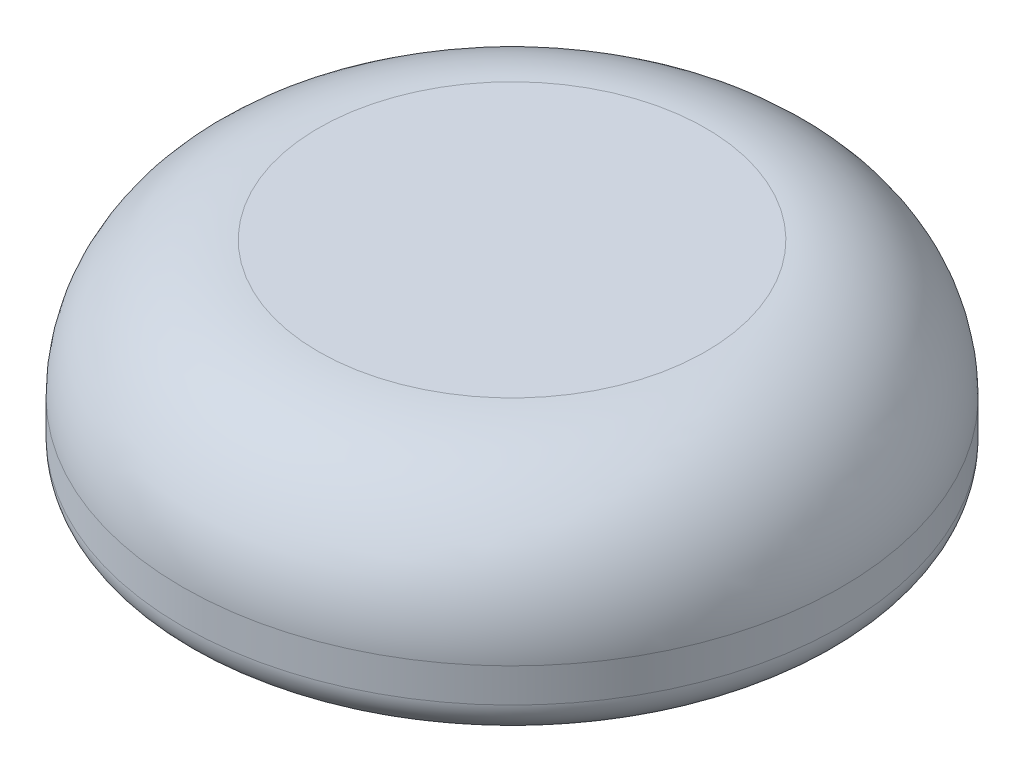
SolidWorks part; units mm, degrees
material "PP Copolymer"
ref_plane "Front Plane" through (0, 0, 0) normal (0, 0, 1) x (1, 0, 0)
ref_plane "Top Plane" through (0, 0, 0) normal (0, 1, 0) x (1, 0, 0)
ref_plane "Right Plane" through (0, 0, 0) normal (1, 0, 0) x (0, 0, -1)
sketch "Sketch3" plane through (0, 0, 0) normal (1, 0, 0) x (0, 0, -1)
  line L0 (12.319, -5.081) -> (12.319, -6.3498)
  line L2 (0, 0) -> (7.238, 0)
  line L4 (10.7952, -7.62) -> (11.0488, -7.62)
  line L5 (9.525, -6.3498) -> (9.525, -4.6834)
  line L7 (0, -2.6086) -> (8.5345, -2.6086)
  line L8 (0, -2.6086) -> (0, 0)
  line L9 (0, -2.6086) -> (0, -10.2365) construction
  arc A0 (12.319, -5.081) -> (7.238, 0) centre (7.238, -5.081) ccw
  arc A2 (9.525, -4.6834) -> (8.5345, -2.6086) centre (8.5345, -3.8824) ccw
  arc A6 (9.525, -6.3498) -> (10.7952, -7.62) centre (10.7952, -6.3498) ccw
  arc A8 (11.0488, -7.62) -> (12.319, -6.3498) centre (11.0488, -6.3498) ccw
  dimension "D3" = 5.081
  dimension "D5" = 1.2702
  dimension "D6" = 1.2702
  dimension "D12" = 1.2738
  dimension "D1" = 12.319
  dimension "D2" = 9.525
  dimension "D4" = 7.62
  dimension "D8" = 2.6086
  dimension "D10" = 4.6834
revolve "Revolve1" add sketch "Sketch3" angle 360 about L9
